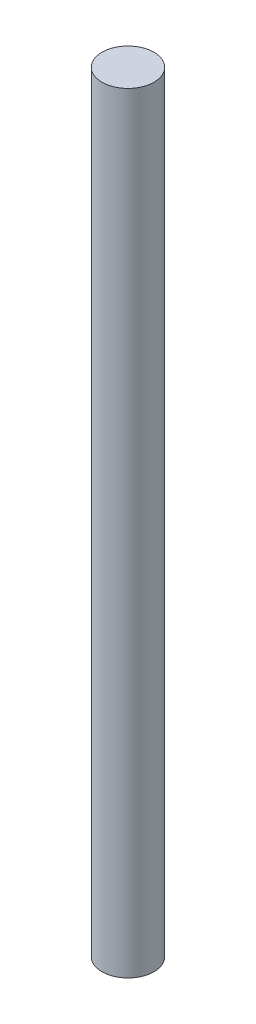
SolidWorks part; units mm, degrees
ref_plane "Front Plane" through (0, 0, 0) normal (0, 0, 1) x (1, 0, 0)
ref_plane "Top Plane" through (0, 0, 0) normal (0, 1, 0) x (1, 0, 0)
ref_plane "Right Plane" through (0, 0, 0) normal (1, 0, 0) x (0, 0, -1)
other "Bounding Box"
ref_plane "Default Plane" through (13.8565, 3.175, 6.7999) normal (0, -1, 0) x (-1, 0, 0)
sketch "Sketch1" plane through (0, 0, 0) normal (0, 1, 0) x (1, 0, 0)
  circle A0 centre (0, 0) radius 1.5
  dimension "D1" = 3
extrude "Boss-Extrude1" add sketch "Sketch1" along normal blind 44.45
